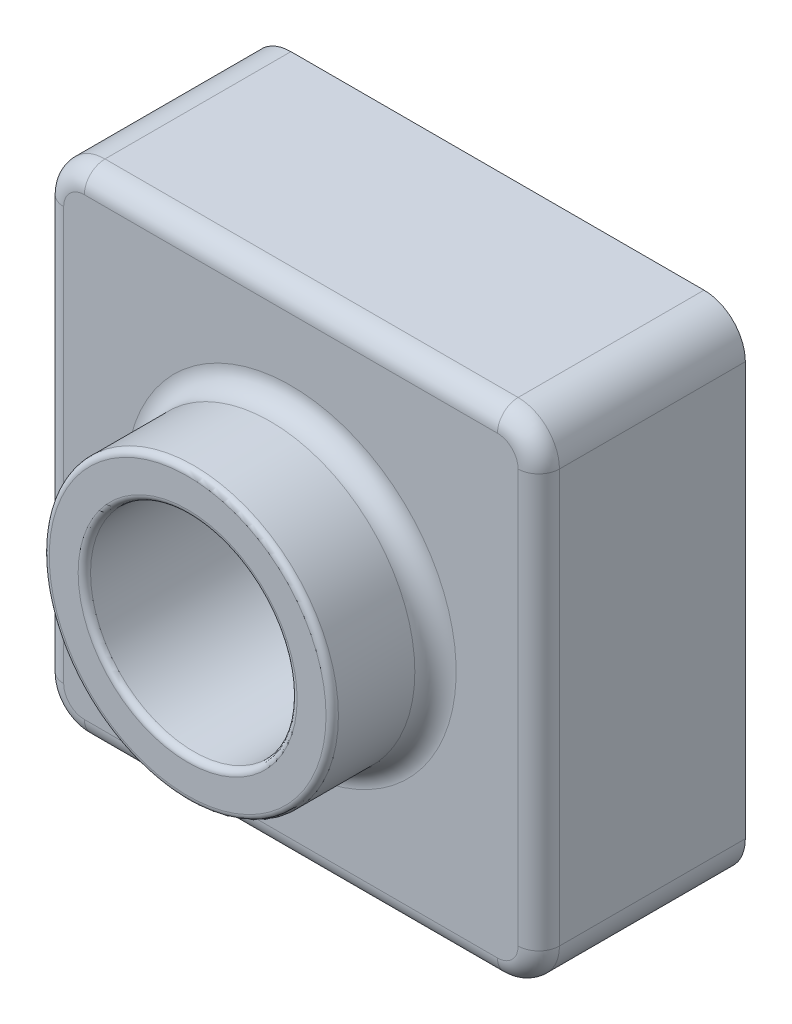
SolidWorks part; units mm, degrees
ref_plane "Front" through (0, 0, 0) normal (0, 0, 1) x (1, 0, 0)
ref_plane "Top" through (0, 0, 0) normal (0, 1, 0) x (1, 0, 0)
ref_plane "Right" through (0, 0, 0) normal (1, 0, 0) x (0, 0, -1)
sketch "Sketch1" plane through (0, 0, 0) normal (0, 0, 1) x (1, 0, 0)
  line L1 (0, 0) -> (120, 0)
  line L2 (0, 0) -> (0, 120)
  line L3 (0, 120) -> (120, 120)
  line L4 (120, 0) -> (120, 120)
  dimension "D1" = 120
  dimension "D2" = 120
extrude "Boss-Extrude1" add sketch "Sketch1" along normal blind 50
sketch "Sketch2" plane through (0, 0, 50) normal (0, 0, 1) x (1, 0, 0)
  line L0 (120, 120) -> (0, 120) construction
  line L1 (120, 0) -> (120, 120) construction
  circle A0 centre (60, 60) radius 35
  dimension "D1" = 70
  dimension "D2" = 60
  dimension "D3" = 60
extrude "Boss-Extrude2" add sketch "Sketch2" along normal blind 25 contours A0
sketch "Sketch6" plane through (0, 0, 75) normal (0, 0, 1) x (1, 0, 0)
  circle A0 centre (60, 60) radius 25
  dimension "D1" = 50
extrude "Cut-Extrude1" cut sketch "Sketch6" against normal through all
fillet "Fillet3" radius 10 4 edges at (120, 0, 25) (0, 0, 25) (0, 120, 25) (120, 120, 25)
fillet "Fillet4" radius 1.5 2 edges at (95, 60, 75) (85, 60, 75)
fillet "Fillet5" radius 5 9 edges at (25, 60, 50) (2.9289, 2.9289, 50) (0, 60, 50) (2.9289, 117.0711, 50) (60, 120, 50) (117.0711, 117.0711, 50) (120, 60, 50) (117.0711, 2.9289, 50) (60, 0, 50)
shell "Shell1" thickness 2
